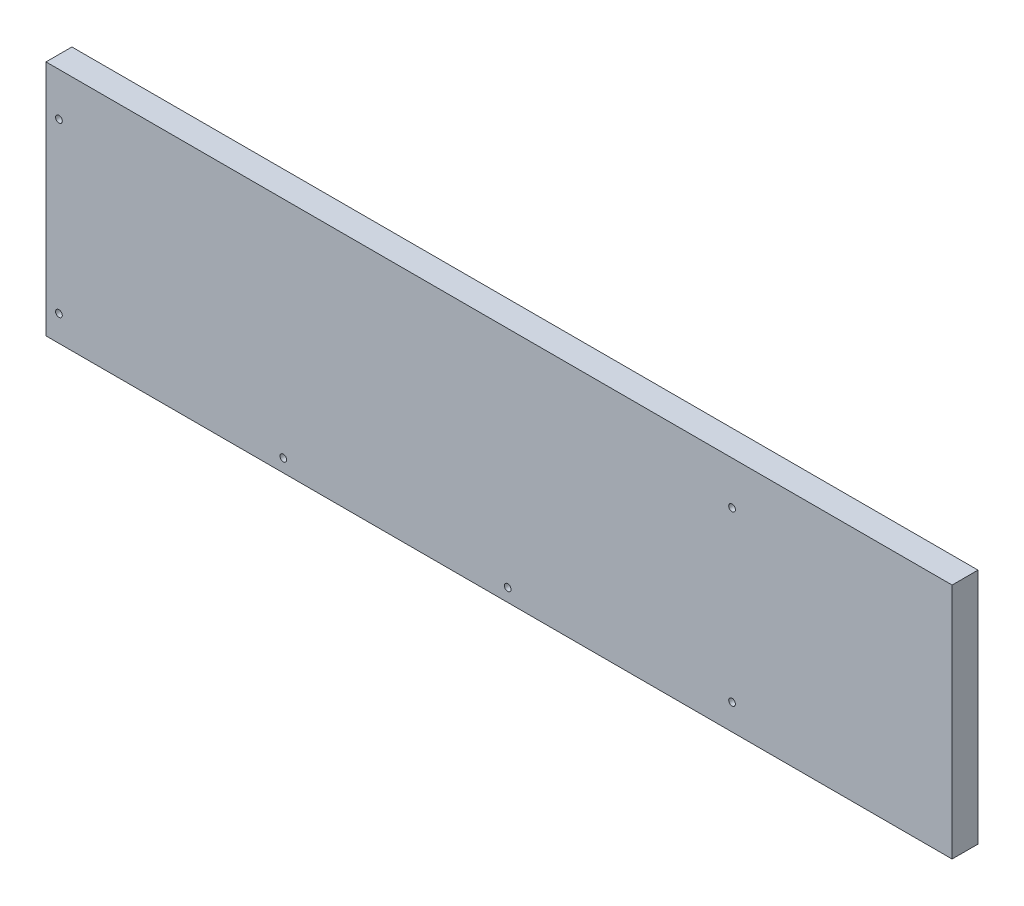
SolidWorks part; units mm, degrees
ref_plane "Front Plane" through (0, 0, 0) normal (0, 0, 1) x (1, 0, 0)
ref_plane "Top Plane" through (0, 0, 0) normal (0, 1, 0) x (1, 0, 0)
ref_plane "Right Plane" through (0, 0, 0) normal (1, 0, 0) x (0, 0, -1)
sketch "Sketch1" plane through (0, 0, 0) normal (0, 0, 1) x (1, 0, 0)
  line L1 (-210, 55) -> (210, 55)
  line L2 (-210, 55) -> (-210, -55)
  line L3 (-210, -55) -> (210, -55)
  line L4 (210, 55) -> (210, -55)
  line L5 (-210, 55) -> (210, -55) construction
  line L6 (-210, -55) -> (210, 55) construction
  point P0 (0, 0)
  dimension "D1" = 420
  dimension "D2" = 110
extrude "Boss-Extrude1" add sketch "Sketch1" along normal blind 12
sketch "Sketch2" plane through (0, 0, 12) normal (0, 0, 1) x (1, 0, 0)
  line L0 (-210, 55) -> (-210, -55) construction
  line L1 (210, 55) -> (-210, 55) construction
  line L2 (-210, -55) -> (210, -55) construction
  circle A0 centre (-204, 35) radius 1.55
  circle A1 centre (-204, -43) radius 1.55
  circle A2 centre (-100, -49) radius 1.55
  circle A3 centre (4, -49) radius 1.55
  circle A4 centre (108, -43) radius 1.55
  circle A5 centre (108, 35) radius 1.55
  dimension "D1" = 3.1
  dimension "D2" = 3.1
  dimension "D3" = 3.1
  dimension "D4" = 3.1
  dimension "D5" = 3.1
  dimension "D6" = 3.1
  dimension "D7" = 6
  dimension "D8" = 6
  dimension "D9" = 20
  dimension "D10" = 12
  dimension "D11" = 6
  dimension "D12" = 110
  dimension "D13" = 6
  dimension "D14" = 104
  dimension "D15" = 318
  dimension "D16" = 12
  dimension "D17" = 318
  dimension "D18" = 20
extrude "Cut-Extrude2" cut sketch "Sketch2" against normal through all
